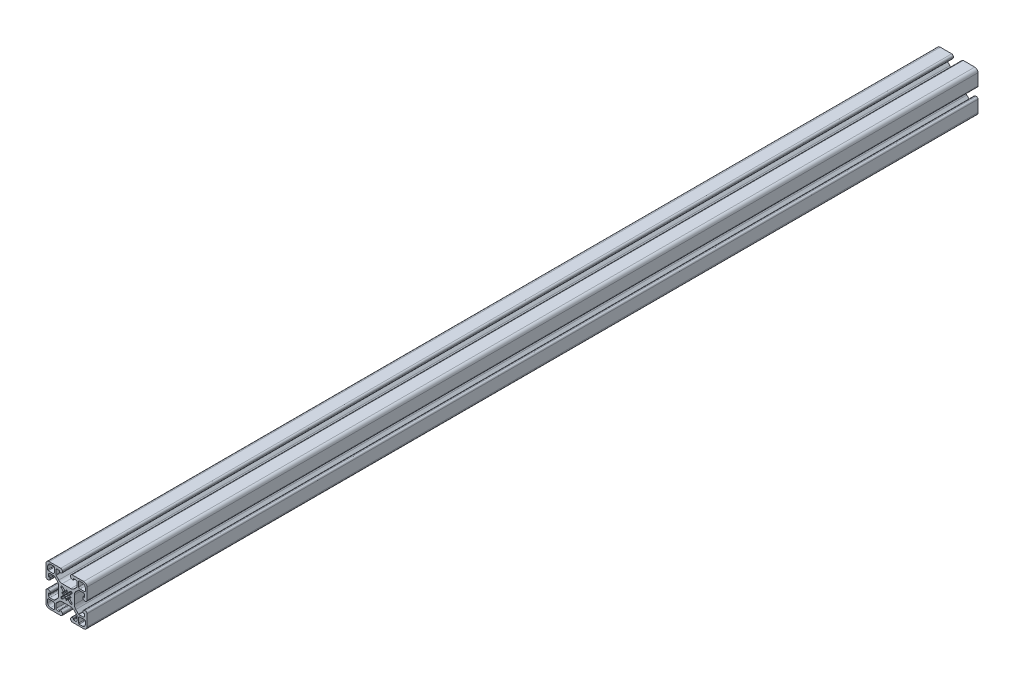
SolidWorks part; units mm, degrees
other "Extrude1"
material "6063-T5"
ref_plane "Front Plane" through (0, 0, 0) normal (0, 0, 1) x (1, 0, 0)
ref_plane "Top Plane" through (0, 0, 0) normal (0, 1, 0) x (1, 0, 0)
ref_plane "Right Plane" through (0, 0, 0) normal (1, 0, 0) x (0, 0, -1)
sketch "Sketch1" plane through (0, 0, 0) normal (0, 0, 1) x (1, 0, 0)
  line L0 (12.4898, -18.345) -> (15.545, -18.345)
  line L1 (11.8598, -13.1298) -> (11.8598, -17.715)
  line L2 (17.715, -11.8598) -> (13.1298, -11.8598)
  line L3 (18.345, -15.545) -> (18.345, -12.4898)
  line L4 (-18.345, -12.4898) -> (-18.345, -15.545)
  line L5 (-13.1298, -11.8598) -> (-17.715, -11.8598)
  line L6 (-11.8598, -17.715) -> (-11.8598, -13.1298)
  line L7 (-15.545, -18.345) -> (-12.4898, -18.345)
  line L8 (18.345, 12.4898) -> (18.345, 15.545)
  line L9 (13.1298, 11.8598) -> (17.715, 11.8598)
  line L10 (11.8598, 17.715) -> (11.8598, 13.1298)
  line L11 (15.545, 18.345) -> (12.4898, 18.345)
  line L12 (-12.4898, 18.345) -> (-15.545, 18.345)
  line L13 (-11.8598, 13.1298) -> (-11.8598, 17.715)
  line L14 (-17.715, 11.8598) -> (-13.1298, 11.8598)
  line L15 (-18.345, 15.545) -> (-18.345, 12.4898)
  line L16 (-5.63, 20) -> (-16.83, 20)
  line L17 (-20, 16.83) -> (-20, 5.63)
  line L18 (-18.43, 4.06) -> (-17.57, 4.06)
  line L19 (-16, 5.63) -> (-16, 6.605)
  line L20 (-16.25, 6.855) -> (-17.25, 6.855)
  line L21 (-17.5, 7.105) -> (-17.5, 9.015)
  line L22 (-16.23, 10.285) -> (-12.2162, 10.285)
  line L23 (-11.5869, 10.0243) -> (-9.0762, 7.5137)
  line L24 (-7.685, 4.1549) -> (-7.685, -4.1549)
  line L25 (-9.0762, -7.5137) -> (-11.5869, -10.0243)
  line L26 (-12.2162, -10.285) -> (-16.23, -10.285)
  line L27 (-17.5, -9.015) -> (-17.5, -7.105)
  line L28 (-17.25, -6.855) -> (-16.25, -6.855)
  line L29 (-16, -6.605) -> (-16, -5.63)
  line L30 (-17.57, -4.06) -> (-18.43, -4.06)
  line L31 (-20, -5.63) -> (-20, -16.83)
  line L32 (-16.83, -20) -> (-5.63, -20)
  line L33 (-4.06, -18.43) -> (-4.06, -17.57)
  line L34 (-5.63, -16) -> (-6.605, -16)
  line L35 (-6.855, -16.25) -> (-6.855, -17.25)
  line L36 (-7.105, -17.5) -> (-9.015, -17.5)
  line L37 (-10.285, -16.23) -> (-10.285, -12.2162)
  line L38 (-10.0243, -11.5869) -> (-7.5137, -9.0762)
  line L39 (-4.1549, -7.685) -> (4.1549, -7.685)
  line L40 (7.5137, -9.0762) -> (10.0243, -11.5869)
  line L41 (10.285, -12.2162) -> (10.285, -16.23)
  line L42 (9.015, -17.5) -> (7.105, -17.5)
  line L43 (6.855, -17.25) -> (6.855, -16.25)
  line L44 (6.605, -16) -> (5.63, -16)
  line L45 (4.06, -17.57) -> (4.06, -18.43)
  line L46 (5.63, -20) -> (16.83, -20)
  line L47 (20, -16.83) -> (20, -5.63)
  line L48 (18.43, -4.06) -> (17.57, -4.06)
  line L49 (16, -5.63) -> (16, -6.605)
  line L50 (16.25, -6.855) -> (17.25, -6.855)
  line L51 (17.5, -7.105) -> (17.5, -9.015)
  line L52 (16.23, -10.285) -> (12.2162, -10.285)
  line L53 (11.5869, -10.0243) -> (9.0762, -7.5137)
  line L54 (7.685, -4.1549) -> (7.685, 4.1549)
  line L55 (9.0762, 7.5137) -> (11.5869, 10.0243)
  line L56 (12.2162, 10.285) -> (16.23, 10.285)
  line L57 (17.5, 9.015) -> (17.5, 7.105)
  line L58 (17.25, 6.855) -> (16.25, 6.855)
  line L59 (16, 6.605) -> (16, 5.63)
  line L60 (17.57, 4.06) -> (18.43, 4.06)
  line L61 (20, 5.63) -> (20, 16.83)
  line L62 (16.83, 20) -> (5.63, 20)
  line L63 (4.06, 18.43) -> (4.06, 17.57)
  line L64 (5.63, 16) -> (6.605, 16)
  line L65 (6.855, 16.25) -> (6.855, 17.25)
  line L66 (7.105, 17.5) -> (9.015, 17.5)
  line L67 (10.285, 16.23) -> (10.285, 12.2162)
  line L68 (10.0243, 11.5869) -> (7.5137, 9.0762)
  line L69 (4.1549, 7.685) -> (-4.1549, 7.685)
  line L70 (-7.5137, 9.0762) -> (-10.0243, 11.5869)
  line L71 (-10.285, 12.2162) -> (-10.285, 16.23)
  line L72 (-9.015, 17.5) -> (-7.105, 17.5)
  line L73 (-6.855, 17.25) -> (-6.855, 16.25)
  line L74 (-6.605, 16) -> (-5.63, 16)
  line L75 (-4.06, 17.57) -> (-4.06, 18.43)
  line L76 (-4.8481, -5.4393) -> (-3.712, -5.1263)
  line L77 (-3.712, -5.1263) -> (-1.5907, -3.0049)
  line L78 (-0.625, -3.3421) -> (-0.4923, -4.0876)
  line L79 (0.4923, -4.0876) -> (0.625, -3.3421)
  line L80 (1.5907, -3.0049) -> (3.712, -5.1263)
  line L81 (3.712, -5.1263) -> (4.8481, -5.4393)
  line L82 (5.4393, -4.8481) -> (5.1263, -3.712)
  line L83 (5.1263, -3.712) -> (3.0049, -1.5907)
  line L84 (3.3421, -0.625) -> (4.0876, -0.4923)
  line L85 (4.0876, 0.4923) -> (3.3421, 0.625)
  line L86 (3.0049, 1.5907) -> (5.1263, 3.712)
  line L87 (5.1263, 3.712) -> (5.4393, 4.8481)
  line L88 (4.8481, 5.4393) -> (3.712, 5.1263)
  line L89 (3.712, 5.1263) -> (1.5907, 3.0049)
  line L90 (0.625, 3.3421) -> (0.4923, 4.0876)
  line L91 (-0.4923, 4.0876) -> (-0.625, 3.3421)
  line L92 (-1.5907, 3.0049) -> (-3.712, 5.1263)
  line L93 (-3.712, 5.1263) -> (-4.8481, 5.4393)
  line L94 (-5.4393, 4.8481) -> (-5.1263, 3.712)
  line L95 (-5.1263, 3.712) -> (-3.0049, 1.5907)
  line L96 (-3.3421, 0.625) -> (-4.0876, 0.4923)
  line L97 (-4.0876, -0.4923) -> (-3.3421, -0.625)
  line L98 (-3.0049, -1.5907) -> (-5.1263, -3.712)
  line L99 (-5.1263, -3.712) -> (-5.4393, -4.8481)
  arc A0 (15.545, -18.345) -> (18.345, -15.545) centre (15.545, -15.545) ccw
  arc A1 (11.8598, -17.715) -> (12.4898, -18.345) centre (12.4898, -17.715) ccw
  arc A2 (13.1298, -11.8598) -> (11.8598, -13.1298) centre (13.1298, -13.1298) ccw
  arc A3 (18.345, -12.4898) -> (17.715, -11.8598) centre (17.715, -12.4898) ccw
  arc A4 (-18.345, -15.545) -> (-15.545, -18.345) centre (-15.545, -15.545) ccw
  arc A5 (-17.715, -11.8598) -> (-18.345, -12.4898) centre (-17.715, -12.4898) ccw
  arc A6 (-11.8598, -13.1298) -> (-13.1298, -11.8598) centre (-13.1298, -13.1298) ccw
  arc A7 (-12.4898, -18.345) -> (-11.8598, -17.715) centre (-12.4898, -17.715) ccw
  arc A8 (18.345, 15.545) -> (15.545, 18.345) centre (15.545, 15.545) ccw
  arc A9 (17.715, 11.8598) -> (18.345, 12.4898) centre (17.715, 12.4898) ccw
  arc A10 (11.8598, 13.1298) -> (13.1298, 11.8598) centre (13.1298, 13.1298) ccw
  arc A11 (12.4898, 18.345) -> (11.8598, 17.715) centre (12.4898, 17.715) ccw
  arc A12 (-15.545, 18.345) -> (-18.345, 15.545) centre (-15.545, 15.545) ccw
  arc A13 (-11.8598, 17.715) -> (-12.4898, 18.345) centre (-12.4898, 17.715) ccw
  arc A14 (-13.1298, 11.8598) -> (-11.8598, 13.1298) centre (-13.1298, 13.1298) ccw
  arc A15 (-18.345, 12.4898) -> (-17.715, 11.8598) centre (-17.715, 12.4898) ccw
  arc A16 (-4.06, 18.43) -> (-5.63, 20) centre (-5.63, 18.43) ccw
  arc A17 (-16.83, 20) -> (-20, 16.83) centre (-16.83, 16.83) ccw
  arc A18 (-20, 5.63) -> (-18.43, 4.06) centre (-18.43, 5.63) ccw
  arc A19 (-17.57, 4.06) -> (-16, 5.63) centre (-17.57, 5.63) ccw
  arc A20 (-16, 6.605) -> (-16.25, 6.855) centre (-16.25, 6.605) ccw
  arc A21 (-17.5, 7.105) -> (-17.25, 6.855) centre (-17.25, 7.105) ccw
  arc A22 (-16.23, 10.285) -> (-17.5, 9.015) centre (-16.23, 9.015) ccw
  arc A23 (-11.5869, 10.0243) -> (-12.2162, 10.285) centre (-12.2162, 9.395) ccw
  arc A24 (-7.685, 4.1549) -> (-9.0762, 7.5137) centre (-12.435, 4.1549) ccw
  arc A25 (-9.0762, -7.5137) -> (-7.685, -4.1549) centre (-12.435, -4.1549) ccw
  arc A26 (-12.2162, -10.285) -> (-11.5869, -10.0243) centre (-12.2162, -9.395) ccw
  arc A27 (-17.5, -9.015) -> (-16.23, -10.285) centre (-16.23, -9.015) ccw
  arc A28 (-17.25, -6.855) -> (-17.5, -7.105) centre (-17.25, -7.105) ccw
  arc A29 (-16.25, -6.855) -> (-16, -6.605) centre (-16.25, -6.605) ccw
  arc A30 (-16, -5.63) -> (-17.57, -4.06) centre (-17.57, -5.63) ccw
  arc A31 (-18.43, -4.06) -> (-20, -5.63) centre (-18.43, -5.63) ccw
  arc A32 (-20, -16.83) -> (-16.83, -20) centre (-16.83, -16.83) ccw
  arc A33 (-5.63, -20) -> (-4.06, -18.43) centre (-5.63, -18.43) ccw
  arc A34 (-4.06, -17.57) -> (-5.63, -16) centre (-5.63, -17.57) ccw
  arc A35 (-6.605, -16) -> (-6.855, -16.25) centre (-6.605, -16.25) ccw
  arc A36 (-7.105, -17.5) -> (-6.855, -17.25) centre (-7.105, -17.25) ccw
  arc A37 (-10.285, -16.23) -> (-9.015, -17.5) centre (-9.015, -16.23) ccw
  arc A38 (-10.0243, -11.5869) -> (-10.285, -12.2162) centre (-9.395, -12.2162) ccw
  arc A39 (-4.1549, -7.685) -> (-7.5137, -9.0762) centre (-4.1549, -12.435) ccw
  arc A40 (7.5137, -9.0762) -> (4.1549, -7.685) centre (4.1549, -12.435) ccw
  arc A41 (10.285, -12.2162) -> (10.0243, -11.5869) centre (9.395, -12.2162) ccw
  arc A42 (9.015, -17.5) -> (10.285, -16.23) centre (9.015, -16.23) ccw
  arc A43 (6.855, -17.25) -> (7.105, -17.5) centre (7.105, -17.25) ccw
  arc A44 (6.855, -16.25) -> (6.605, -16) centre (6.605, -16.25) ccw
  arc A45 (5.63, -16) -> (4.06, -17.57) centre (5.63, -17.57) ccw
  arc A46 (4.06, -18.43) -> (5.63, -20) centre (5.63, -18.43) ccw
  arc A47 (16.83, -20) -> (20, -16.83) centre (16.83, -16.83) ccw
  arc A48 (20, -5.63) -> (18.43, -4.06) centre (18.43, -5.63) ccw
  arc A49 (17.57, -4.06) -> (16, -5.63) centre (17.57, -5.63) ccw
  arc A50 (16, -6.605) -> (16.25, -6.855) centre (16.25, -6.605) ccw
  arc A51 (17.5, -7.105) -> (17.25, -6.855) centre (17.25, -7.105) ccw
  arc A52 (16.23, -10.285) -> (17.5, -9.015) centre (16.23, -9.015) ccw
  arc A53 (11.5869, -10.0243) -> (12.2162, -10.285) centre (12.2162, -9.395) ccw
  arc A54 (7.685, -4.1549) -> (9.0762, -7.5137) centre (12.435, -4.1549) ccw
  arc A55 (9.0762, 7.5137) -> (7.685, 4.1549) centre (12.435, 4.1549) ccw
  arc A56 (12.2162, 10.285) -> (11.5869, 10.0243) centre (12.2162, 9.395) ccw
  arc A57 (17.5, 9.015) -> (16.23, 10.285) centre (16.23, 9.015) ccw
  arc A58 (17.25, 6.855) -> (17.5, 7.105) centre (17.25, 7.105) ccw
  arc A59 (16.25, 6.855) -> (16, 6.605) centre (16.25, 6.605) ccw
  arc A60 (16, 5.63) -> (17.57, 4.06) centre (17.57, 5.63) ccw
  arc A61 (18.43, 4.06) -> (20, 5.63) centre (18.43, 5.63) ccw
  arc A62 (20, 16.83) -> (16.83, 20) centre (16.83, 16.83) ccw
  arc A63 (5.63, 20) -> (4.06, 18.43) centre (5.63, 18.43) ccw
  arc A64 (4.06, 17.57) -> (5.63, 16) centre (5.63, 17.57) ccw
  arc A65 (6.605, 16) -> (6.855, 16.25) centre (6.605, 16.25) ccw
  arc A66 (7.105, 17.5) -> (6.855, 17.25) centre (7.105, 17.25) ccw
  arc A67 (10.285, 16.23) -> (9.015, 17.5) centre (9.015, 16.23) ccw
  arc A68 (10.0243, 11.5869) -> (10.285, 12.2162) centre (9.395, 12.2162) ccw
  arc A69 (4.1549, 7.685) -> (7.5137, 9.0762) centre (4.1549, 12.435) ccw
  arc A70 (-7.5137, 9.0762) -> (-4.1549, 7.685) centre (-4.1549, 12.435) ccw
  arc A71 (-10.285, 12.2162) -> (-10.0243, 11.5869) centre (-9.395, 12.2162) ccw
  arc A72 (-9.015, 17.5) -> (-10.285, 16.23) centre (-9.015, 16.23) ccw
  arc A73 (-6.855, 17.25) -> (-7.105, 17.5) centre (-7.105, 17.25) ccw
  arc A74 (-6.855, 16.25) -> (-6.605, 16) centre (-6.605, 16.25) ccw
  arc A75 (-5.63, 16) -> (-4.06, 17.57) centre (-5.63, 17.57) ccw
  arc A76 (-1.5907, -3.0049) -> (-0.625, -3.3421) centre (0, 0) ccw
  arc A77 (-0.4923, -4.0876) -> (0.4923, -4.0876) centre (0, -4) ccw
  arc A78 (0.625, -3.3421) -> (1.5907, -3.0049) centre (0, 0) ccw
  arc A79 (4.8481, -5.4393) -> (5.4393, -4.8481) centre (4.9497, -4.9497) ccw
  arc A80 (3.0049, -1.5907) -> (3.3421, -0.625) centre (0, 0) ccw
  arc A81 (4.0876, -0.4923) -> (4.0876, 0.4923) centre (4, 0) ccw
  arc A82 (3.3421, 0.625) -> (3.0049, 1.5907) centre (0, 0) ccw
  arc A83 (5.4393, 4.8481) -> (4.8481, 5.4393) centre (4.9497, 4.9497) ccw
  arc A84 (1.5907, 3.0049) -> (0.625, 3.3421) centre (0, 0) ccw
  arc A85 (0.4923, 4.0876) -> (-0.4923, 4.0876) centre (0, 4) ccw
  arc A86 (-0.625, 3.3421) -> (-1.5907, 3.0049) centre (0, 0) ccw
  arc A87 (-4.8481, 5.4393) -> (-5.4393, 4.8481) centre (-4.9497, 4.9497) ccw
  arc A88 (-3.0049, 1.5907) -> (-3.3421, 0.625) centre (0, 0) ccw
  arc A89 (-4.0876, 0.4923) -> (-4.0876, -0.4923) centre (-4, 0) ccw
  arc A90 (-3.3421, -0.625) -> (-3.0049, -1.5907) centre (0, 0) ccw
  arc A91 (-5.4393, -4.8481) -> (-4.8481, -5.4393) centre (-4.9497, -4.9497) ccw
extrude "Extrude1" add sketch "Sketch1" against normal blind 870
